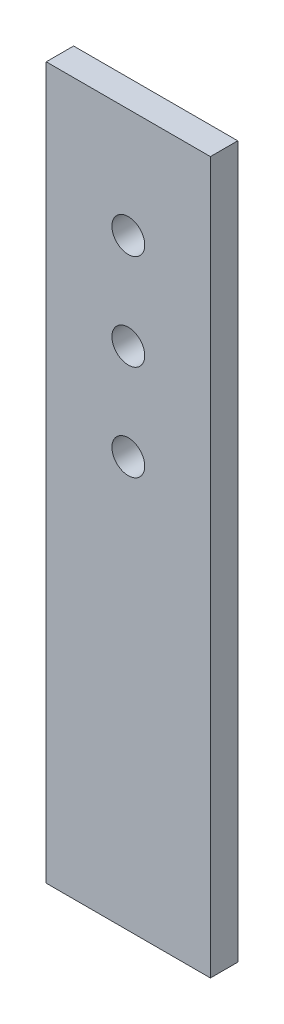
SolidWorks part; units mm, degrees
ref_plane "Alzado" through (0, 0, 0) normal (0, 0, 1) x (1, 0, 0)
ref_plane "Planta" through (0, 0, 0) normal (0, 1, 0) x (1, 0, 0)
ref_plane "Vista lateral" through (0, 0, 0) normal (1, 0, 0) x (0, 0, -1)
sketch "Croquis1" plane through (0, 0, 0) normal (0, 0, 1) x (1, 0, 0)
  line L0 (-30, 55) -> (30, 55) construction
  line L1 (-30, 130) -> (30, 130)
  line L2 (-30, 130) -> (-30, -130)
  line L3 (-30, -130) -> (30, -130)
  line L4 (30, 130) -> (30, -130)
  line L5 (-30, 130) -> (30, -130) construction
  line L6 (-30, -130) -> (30, 130) construction
  line L7 (0, 130) -> (0, -130) construction
  line L8 (-30, 20) -> (30, 20) construction
  line L9 (-30, 90) -> (30, 90) construction
  circle A0 centre (0, 55) radius 6
  circle A1 centre (0, 90) radius 6
  circle A2 centre (0, 20) radius 6
  point P0 (0, 0)
  dimension "D4" = 12
  dimension "D7" = 12
  dimension "D8" = 12
  dimension "D1" = 60
  dimension "D2" = 260
  dimension "D3" = 75
  dimension "D5" = 35
  dimension "D6" = 35
extrude "Saliente-Extruir1" add sketch "Croquis1" along normal blind 10
